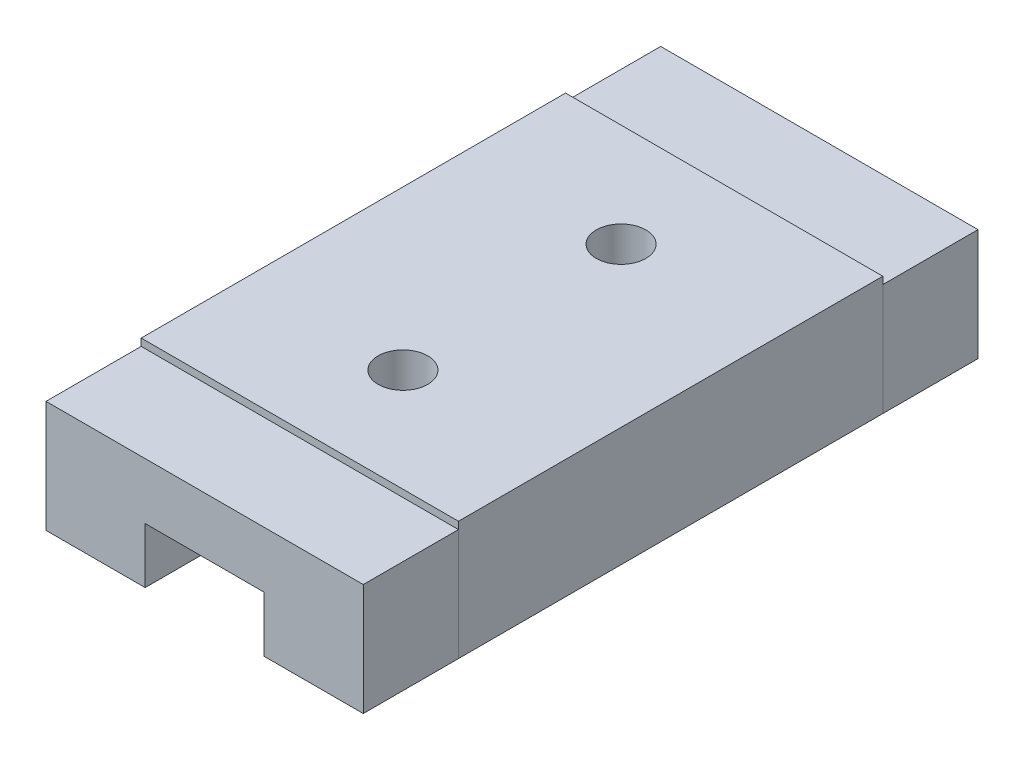
SolidWorks part; units mm, degrees
ref_plane "Front" through (0, 0, 0) normal (0, 0, 1) x (1, 0, 0)
ref_plane "Top" through (0, 0, 0) normal (0, 1, 0) x (1, 0, 0)
ref_plane "Right" through (0, 0, 0) normal (1, 0, 0) x (0, 0, -1)
sketch "Sketch1" plane through (0, 0, 0) normal (0, 0, 1) x (1, 0, 0)
  line L0 (-1.5, -1.5) -> (-1.5, -0.1)
  line L1 (-4, -1.5) -> (-1.5, -1.5)
  line L2 (-4, -1.5) -> (-4, 1.5)
  line L3 (-4, 1.5) -> (4, 1.5)
  line L4 (4, -1.5) -> (4, 1.5)
  line L5 (-4, -1.5) -> (4, 1.5) construction
  line L6 (-4, 1.5) -> (4, -1.5) construction
  line L7 (-1.5, -0.1) -> (1.5, -0.1)
  line L8 (1.5, -0.1) -> (1.5, -1.5)
  line L9 (1.5, -1.5) -> (4, -1.5)
  point P0 (0, 0)
  dimension "D1" = 8
  dimension "D2" = 3
  dimension "D3" = 1.4
  dimension "D4" = 3
extrude "Boss-Extrude1" add sketch "Sketch1" along normal blind 10.7
hole_wizard "M1.6x0.35 Tapped Hole1" positions "Sketch2" profile "Sketch3" tap size "M1.6x0.35" standard "ANSI Metric"
sketch "Sketch2" plane through (0, 1.5, 0) normal (0, 1, 0) x (1, 0, 0)
  line L2 (4, 0) -> (-4, 0) construction
  point P0 (0, -2.6)
  point P2 (0, -8.1)
  dimension "D1" = 5.5
  dimension "D2" = 2.6
sketch "Sketch3" plane through (0, 1.5, 2.6) normal (1, 0, 0) x (0, 0, 1)
  line L0 (0, 0) -> (0, 3.5755)
  line L1 (0, 3.5755) -> (0.625, 3.2)
  line L2 (0.625, 3.2) -> (0.625, 0)
  line L5 (0.625, 0) -> (0, 0)
  line L10 (0, 3.5755) -> (-0.625, 3.2) construction
  line L11 (0, -6.35) -> (0, 107.95) construction
  dimension "Tap Drill Dia." = 1.25
  dimension "Tap Drill Depth" = 3.2
  dimension "Drill Angle" = 118
cosmetic thread "Hole Thread2" parameters "D1"=2.4, "D2"=1.6
cosmetic thread "Hole Thread3" parameters "D1"=2.4, "D2"=1.6
sketch "Sketch4" plane through (0, 0, 0) normal (0, 0, -1) x (-1, 0, 0)
  line L0 (-4, 1.3179) -> (4, 1.3179)
  line L1 (-4, -1.5) -> (-4, 1.5) construction
  line L2 (4, 1.5) -> (4, -1.5) construction
  line L3 (4, 1.3179) -> (4, -1.5)
  line L4 (4, -1.5) -> (1.5, -1.5)
  line L5 (1.5, -1.5) -> (1.5, -0.1)
  line L6 (1.5, -0.1) -> (-1.5, -0.1)
  line L7 (-1.5, -0.1) -> (-1.5, -1.5)
  line L8 (-1.5, -1.5) -> (-4, -1.5)
  line L9 (-4, -1.5) -> (-4, 1.3179)
extrude "Boss-Extrude2" add sketch "Sketch4" along normal blind 2.4 separate body
sketch "Sketch5" plane through (0, 0, 10.7) normal (0, 0, 1) x (1, 0, 0)
  line L0 (-4, 1.3179) -> (4, 1.3179)
  line L1 (4, 1.3179) -> (4, -1.5)
  line L2 (1.5, -1.5) -> (4, -1.5) construction
  line L3 (4, -1.5) -> (1.5, -1.5)
  line L4 (1.5, -1.5) -> (1.5, -0.1)
  line L5 (1.5, -0.1) -> (-1.5, -0.1)
  line L6 (-1.5, -0.1) -> (-1.5, -1.5)
  line L7 (-1.5, -1.5) -> (-4, -1.5)
  line L8 (-4, -1.5) -> (-4, 1.3179)
extrude "Boss-Extrude3" add sketch "Sketch5" along normal blind 2.4 separate body
